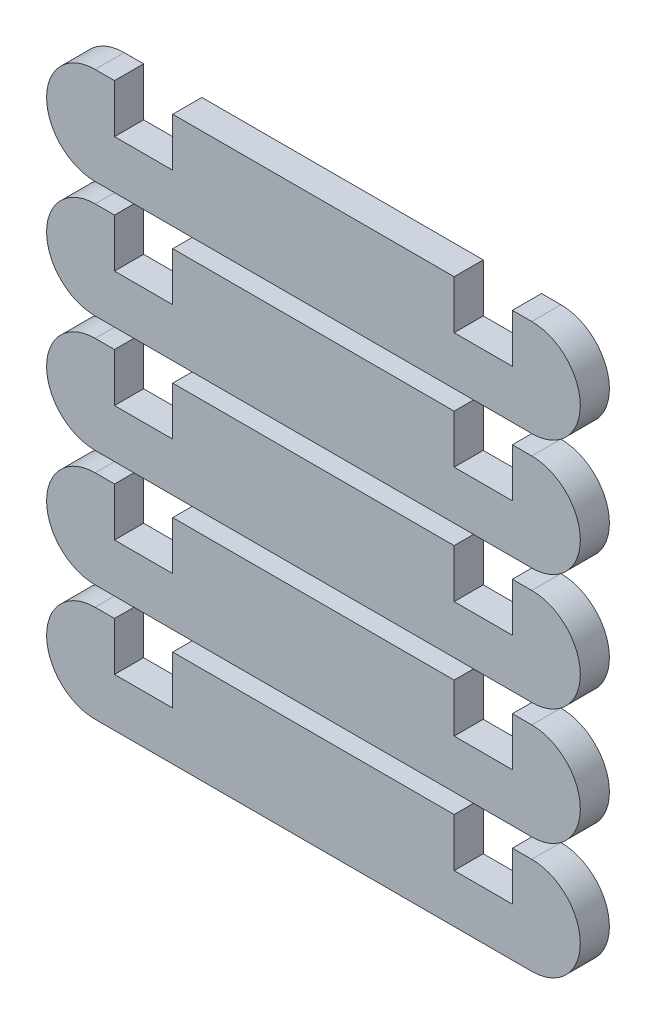
SolidWorks part; units mm, degrees
ref_plane "Front Plane" through (0, 0, 0) normal (0, 0, 1) x (1, 0, 0)
ref_plane "Top Plane" through (0, 0, 0) normal (0, 1, 0) x (1, 0, 0)
ref_plane "Right Plane" through (0, 0, 0) normal (1, 0, 0) x (0, 0, -1)
sketch "Sketch2" plane through (0, 0, 0) normal (0, 0, 1) x (1, 0, 0)
  line L0 (0, 93.5325) -> (0, -82.0761) construction
  line L1 (-110.853, 0) -> (105.2015, 0) construction
  line L3 (-22.5, 5) -> (-20.5, 5)
  line L5 (-22.5, -5) -> (22.5, -5)
  line L12 (20.5, 5) -> (22.5, 5)
  line L13 (-14.5, 5) -> (14.5, 5)
  line L14 (-20.5, 5) -> (-20.5, 0)
  line L15 (-20.5, 0) -> (-14.5, 0)
  line L16 (-14.5, 0) -> (-14.5, 5)
  line L17 (14.5, 5) -> (14.5, 0)
  line L18 (14.5, 0) -> (20.5, 0)
  line L19 (20.5, 0) -> (20.5, 5)
  arc A0 (-22.5, 5) -> (-22.5, -5) centre (-22.5, 0) ccw
  arc A1 (22.5, -5) -> (22.5, 5) centre (22.5, 0) ccw
  point P19 (0, 0)
  dimension "D5" = 5
  dimension "D6" = 5
  dimension "D3" = 5
  dimension "D1" = 22.5
  dimension "D2" = 45
  dimension "D4" = 5
  dimension "D7" = 5
  dimension "D8" = 10
  dimension "D9" = 14.5
  dimension "D10" = 6
  dimension "D11" = 14.5
  dimension "D12" = 6
extrude "Boss-Extrude4" add sketch "Sketch2" along normal blind 3
pattern_linear "LPattern1" count 5 spacing 12 along (0, 1, 0) of bodies 104
